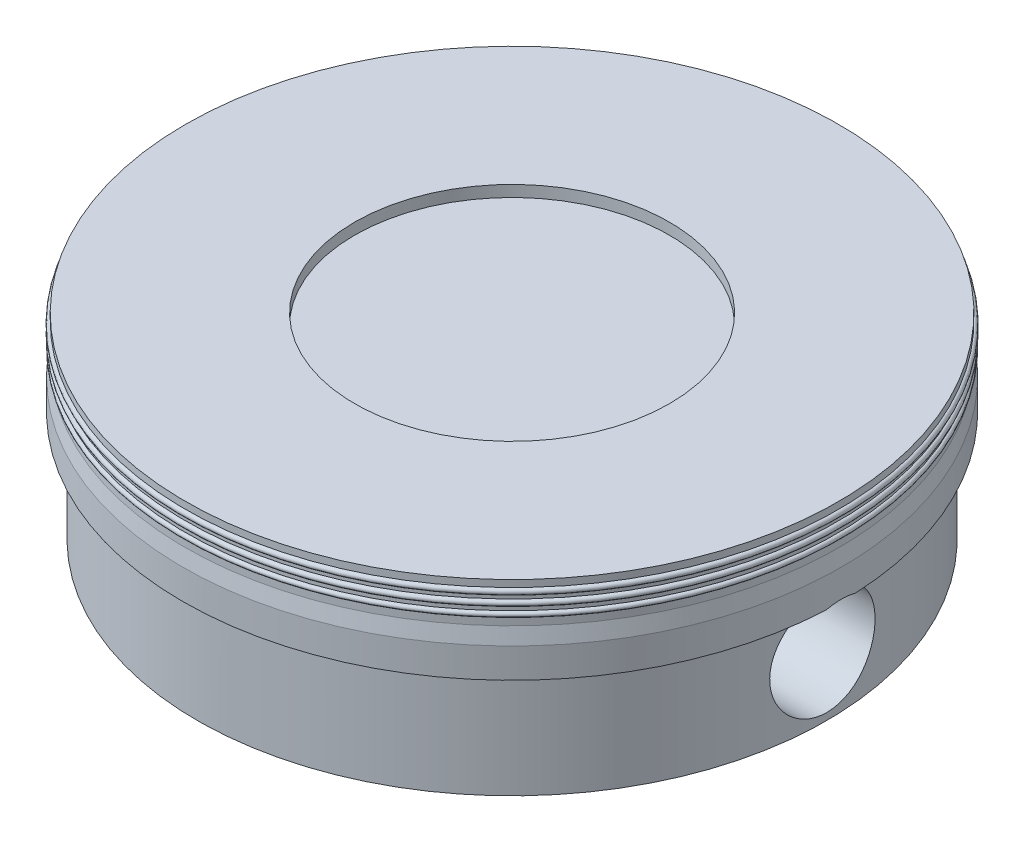
SolidWorks part; units mm, degrees
ref_plane "Front Plane" through (0, 0, 0) normal (0, 0, 1) x (1, 0, 0)
ref_plane "Top Plane" through (0, 0, 0) normal (0, 1, 0) x (1, 0, 0)
ref_plane "Right Plane" through (0, 0, 0) normal (1, 0, 0) x (0, 0, -1)
sketch "Sketch2" plane through (0, 0, 0) normal (0, 0, 1) x (1, 0, 0)
  line L0 (0, 30) -> (0, 0) construction
  line L1 (0, 0) -> (50, 0) construction
  line L2 (47.8, 0) -> (34.3, 0)
  line L3 (34.3, 0) -> (34.3, 19.3)
  line L4 (34.3, 19.3) -> (42, 19.3)
  line L5 (42, 19.3) -> (42, 23.3)
  line L6 (42, 23.3) -> (0, 23.3)
  line L7 (0, 23.3) -> (0, 28)
  line L8 (0, 28) -> (23.9, 28)
  line L9 (23.9, 28) -> (23.9, 29.72)
  line L10 (23.9, 29.72) -> (49.6, 29.72)
  line L11 (49.6, 29.72) -> (49.6, 28.6717)
  line L12 (49.6, 23.6268) -> (50, 21.2661)
  line L13 (50, 21.2661) -> (50, 16.75)
  line L14 (50, 16.75) -> (47.8, 16.75)
  line L15 (47.8, 16.75) -> (47.8, 0)
  line L16 (49.6, 27.7683) -> (49.6, 27.1631)
  line L17 (49.6, 26.2769) -> (49.6, 25.62)
  line L18 (49.6, 24.82) -> (49.6, 23.6268)
  arc A0 (49.6, 27.7683) -> (49.6, 28.6717) centre (49.6, 28.22) ccw
  arc A1 (49.6, 26.2769) -> (49.6, 27.1631) centre (49.6, 26.72) ccw
  arc A2 (49.6, 24.82) -> (49.6, 25.62) centre (49.6, 25.22) ccw
  dimension "D14" = 1.5
  dimension "D1" = 50
  dimension "D2" = 30
  dimension "D3" = 49.6
  dimension "D4" = 0.4
  dimension "D5" = 2.2
  dimension "D6" = 16.75
  dimension "D7" = 13.5
  dimension "D8" = 19.3
  dimension "D9" = 4
  dimension "D10" = 25.7
  dimension "D11" = 1.72
  dimension "D12" = 4.7
  dimension "D13" = 42
  dimension "D15" = 1.5
  dimension "D16" = 1.5
  dimension "D17" = 2.3944
  dimension "D18" = 4.5161
revolve "Revolve1" add sketch "Sketch2" angle 360 about L0
sketch "Sketch3" plane through (0, 0, 0) normal (0, -1, 0) x (1, 0, 0)
  line L0 (0, 34.3) -> (0, 0) construction
  line L1 (0, 0) -> (-34.3, 0) construction
  line L2 (-17.5, 29.4998) -> (-17.5, -29.4998)
  line L3 (17.5, 29.4998) -> (17.5, -29.4998)
  circle A0 centre (0, 0) radius 34.3 construction
  arc A1 (-17.5, 29.4998) -> (-17.5, -29.4998) centre (0, 0) ccw
  arc A2 (17.5, -29.4998) -> (17.5, 29.4998) centre (0, 0) ccw
  dimension "D1" = 35
extrude "Boss-Extrude1" add sketch "Sketch3" against normal up to next
sketch "Sketch4" plane through (0, 0, 0) normal (1, 0, 0) x (0, 0, -1)
  circle A0 centre (0, 9.065) radius 8
  dimension "D1" = 16
  dimension "D2" = 9.065
extrude "Cut-Extrude1" cut sketch "Sketch4" against normal through all both and the other way through all
scale "Scale1" scale about centroid uniform scaling yes scale factor 0.1
